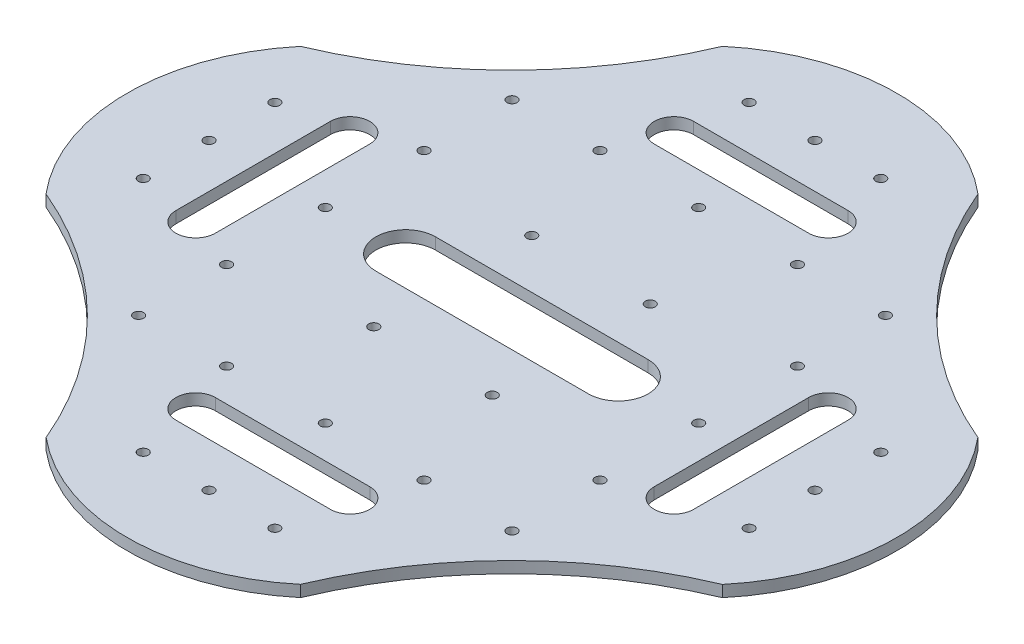
SolidWorks part; units mm, degrees
material "Thornel Mat VMA"
ref_plane "前视基准面" through (0, 0, 0) normal (0, 0, 1) x (1, 0, 0)
ref_plane "上视基准面" through (0, 0, 0) normal (0, 1, 0) x (1, 0, 0)
ref_plane "右视基准面" through (0, 0, 0) normal (1, 0, 0) x (0, 0, -1)
sketch "草图2" plane through (0, 0, 0) normal (0, 1, 0) x (1, 0, 0)
  line L0 (6.6365, 27.504) -> (-106.8107, -85.9432)
  line L1 (-106.8107, 27.504) -> (6.6365, 27.504)
  line L2 (-106.8107, 27.504) -> (-106.8107, -85.9432)
  line L3 (-106.8107, -85.9432) -> (6.6365, -85.9432)
  line L4 (6.6365, 27.504) -> (6.6365, -85.9432)
  line L5 (-106.8107, 27.504) -> (6.6365, -85.9432) construction
  line L6 (-106.8107, -85.9432) -> (6.6365, 27.504) construction
  line L7 (6.6365, -85.9432) -> (-106.8107, 27.504)
  line L8 (-50.0871, -85.9432) -> (-50.0871, -29.2196)
  line L9 (6.6365, -85.9432) -> (99.1639, -178.6774)
  line L10 (99.1639, -178.6774) -> (-199.5448, -178.4707)
  line L11 (-199.5448, -178.4707) -> (-199.3381, 120.2381)
  line L12 (-199.3381, 120.2381) -> (99.3707, 120.0314)
  line L13 (99.3707, 120.0314) -> (99.1639, -178.6774)
  line L14 (6.6365, 27.504) -> (6.6365, 31.004)
  line L15 (-106.8107, 27.504) -> (-106.8107, 31.004)
  line L16 (-106.8107, -85.9432) -> (-110.3107, -85.9432)
  line L17 (6.6365, -85.9432) -> (10.1365, -85.9432)
  line L18 (6.6365, 27.504) -> (10.1365, 27.504)
  line L19 (-50.0871, 27.504) -> (-50.0871, 43.442) construction
  line L20 (-73.555, 43.442) -> (-26.6191, 43.442) construction
  line L21 (-73.555, 49.4168) -> (-26.6191, 49.4168)
  line L22 (-73.555, 37.4672) -> (-26.6191, 37.4672)
  line L23 (-50.0871, 43.442) -> (-50.0871, 62.8305) construction
  line L24 (-50.0871, 62.8305) -> (-30.0871, 62.8305) construction
  line L25 (-50.0871, 27.504) -> (-20.0871, 27.504)
  line L26 (-122.7487, -5.7517) -> (-122.7487, -52.6876) construction
  line L27 (-128.7235, -5.7517) -> (-128.7235, -52.6876)
  line L28 (-116.7739, -5.7517) -> (-116.7739, -52.6876)
  line L29 (22.5745, -52.6876) -> (22.5745, -5.7517) construction
  line L30 (28.5493, -52.6876) -> (28.5493, -5.7517)
  line L31 (16.5997, -52.6876) -> (16.5997, -5.7517)
  line L32 (-26.6191, -101.8813) -> (-73.555, -101.8813) construction
  line L33 (-26.6191, -107.8561) -> (-73.555, -107.8561)
  line L34 (-26.6191, -95.9065) -> (-73.555, -95.9065)
  line L35 (-82.3857, -29.2196) -> (-17.7885, -29.2196) construction
  line L38 (-17.7885, -29.8888) -> (-17.7885, -28.5505) construction
  line L39 (-82.3857, -20.1733) -> (-17.7885, -20.1733)
  line L40 (-82.3857, -38.2659) -> (-17.7885, -38.2659)
  arc A0 (-20.836, -178.5943) -> (99.247, -58.6774) centre (99.1639, -178.6774) cw
  arc A1 (-79.3381, -178.5943) -> (-199.4212, -58.6774) centre (-199.3381, -178.6774) ccw
  arc A2 (99.2876, 0.0314) -> (-20.6293, 120.1144) centre (99.3707, 120.0314) cw
  arc A3 (-199.4618, 0.0314) -> (-79.5449, 120.1144) centre (-199.5448, 120.0314) ccw
  circle A4 centre (6.6365, -85.9432) radius 3.5
  circle A5 centre (6.6365, 27.504) radius 3.5
  circle A6 centre (-106.8107, -85.9432) radius 3.5
  arc A7 (-110.3107, -85.9432) -> (10.1365, -85.9432) centre (-50.0871, -85.9432) ccw
  arc A8 (6.6365, -89.4432) -> (6.6365, 31.004) centre (6.6365, -29.2196) ccw
  arc A9 (-106.8107, -89.4432) -> (-106.8107, 31.004) centre (-106.8107, -29.2196) cw
  arc A10 (-110.3107, 27.504) -> (10.1365, 27.504) centre (-50.0871, 27.504) cw
  circle A11 centre (-106.8107, 27.504) radius 3.5
  circle A12 centre (-106.8107, -85.9432) radius 1.52
  circle A13 centre (6.6365, -85.9432) radius 1.52
  circle A14 centre (6.6365, 27.504) radius 1.52
  circle A15 centre (-106.8107, 27.504) radius 1.52
  arc A16 (-73.555, 49.4168) -> (-73.555, 37.4672) centre (-73.555, 43.442) ccw
  arc A17 (-26.6191, 37.4672) -> (-26.6191, 49.4168) centre (-26.6191, 43.442) ccw
  circle A18 centre (-30.0871, 62.8305) radius 1.52
  circle A19 centre (-50.0871, 62.8305) radius 1.52
  circle A20 centre (-50.0871, 27.504) radius 1.52
  circle A21 centre (-20.0871, 27.504) radius 1.52
  circle A22 centre (-70.0871, 62.8305) radius 1.52
  circle A23 centre (-80.0871, 27.504) radius 1.52
  circle A24 centre (-106.8107, -59.2196) radius 1.52
  circle A25 centre (-106.8107, 0.7804) radius 1.52
  circle A26 centre (-106.8107, -29.2196) radius 1.52
  arc A27 (-128.7235, -5.7517) -> (-116.7739, -5.7517) centre (-122.7487, -5.7517) cw
  arc A28 (-116.7739, -52.6876) -> (-128.7235, -52.6876) centre (-122.7487, -52.6876) cw
  circle A29 centre (-142.1373, -9.2196) radius 1.52
  circle A30 centre (-142.1373, -29.2196) radius 1.52
  circle A31 centre (-142.1373, -49.2196) radius 1.52
  circle A32 centre (41.9631, -49.2196) radius 1.52
  circle A33 centre (41.9631, -29.2196) radius 1.52
  circle A34 centre (41.9631, -9.2196) radius 1.52
  circle A35 centre (6.6365, -29.2196) radius 1.52
  circle A36 centre (-80.0871, -85.9432) radius 1.52
  circle A37 centre (-20.0871, -85.9432) radius 1.52
  circle A38 centre (-50.0871, -85.9432) radius 1.52
  circle A39 centre (-30.0871, -121.2698) radius 1.52
  circle A40 centre (-50.0871, -121.2698) radius 1.52
  circle A41 centre (6.6365, 0.7804) radius 1.52
  circle A42 centre (6.6365, -59.2196) radius 1.52
  arc A43 (28.5493, -52.6876) -> (16.5997, -52.6876) centre (22.5745, -52.6876) cw
  arc A44 (16.5997, -5.7517) -> (28.5493, -5.7517) centre (22.5745, -5.7517) cw
  arc A45 (-26.6191, -107.8561) -> (-26.6191, -95.9065) centre (-26.6191, -101.8813) ccw
  arc A46 (-73.555, -95.9065) -> (-73.555, -107.8561) centre (-73.555, -101.8813) ccw
  circle A47 centre (-70.0871, -121.2698) radius 1.52
  arc A50 (-82.3857, -20.1733) -> (-82.3857, -38.2659) centre (-82.3857, -29.2196) ccw
  arc A51 (-17.7885, -38.2659) -> (-17.7885, -20.1733) centre (-17.7885, -29.2196) ccw
  point P0 (-50.0871, -29.2196)
  point P50 (-50.0871, 43.442)
  point P67 (-122.7487, -29.2196)
  point P100 (22.5745, -29.2196)
  point P107 (-50.0871, -101.8813)
  point P119 (-50.0871, -29.2196)
  dimension "D1" = 20
  dimension "D5" = 30
  dimension "D2" = 3.5
  dimension "D3" = 3.5
  dimension "D4" = 3.5
extrude "凸台-拉伸3" add sketch "草图2" along normal blind 3.5 contours A11 A10 A9 A3 A1 A7 A6 L2 | A11 L2 A6 L0 L7 | A6 L3 L8 L0 | A4 L7 L8 L3 | A6 A9 A7 A1 A0 L9 A8 A4 L3 | A5 L0 L7 A4 L4 | A11 L1 A5 A8 A10 A2 A3 A9 | A9 A10 A3 | A9 A6 A7 | A12 L3 A6 L0 | A12 L0 A6 L2 | A11 A9 A10 | A15 L1 A11 L2 | A15 L7 A11 L1 | A10 A8 A5 | A8 A10 A5 L4 A4 A7 A0 A2 | A2 A10 A8 | A7 A0 L9 | A8 A7 L9 A0 | A13 L3 A4 L9 | A4 A8 L9 | L9 A8 A7 A4 | A13 L4 A4 L7 | A13 L7 A4 L3 | A12 L2 A6 L16 | A13 L9 A4 L17 | A15 L1 A11 L15 | A13 L17 A4 L4 | A11 L7 L0 A5 L1 | A14 L14 A5 L1 | A14 L18 A5 L14 | A14 L4 A5 L18 | A14 L0 A5 L4 | A14 L1 A5 L0 | A12 L16 A6 L3 | A15 L2 A11 L7 | A7 A9 A1
sketch "草图4" plane through (0, 7.25, 0) normal (0, -1, 0) x (1, 0, 0)
  circle A0 centre (-68.0871, 5.2196) radius 1.52
  circle A1 centre (-32.0871, 5.2196) radius 1.52
  circle A2 centre (-68.0871, 53.2196) radius 1.52
  circle A3 centre (-32.0871, 53.2196) radius 1.52
extrude "切除-拉伸2" cut sketch "草图4" along normal blind 59
